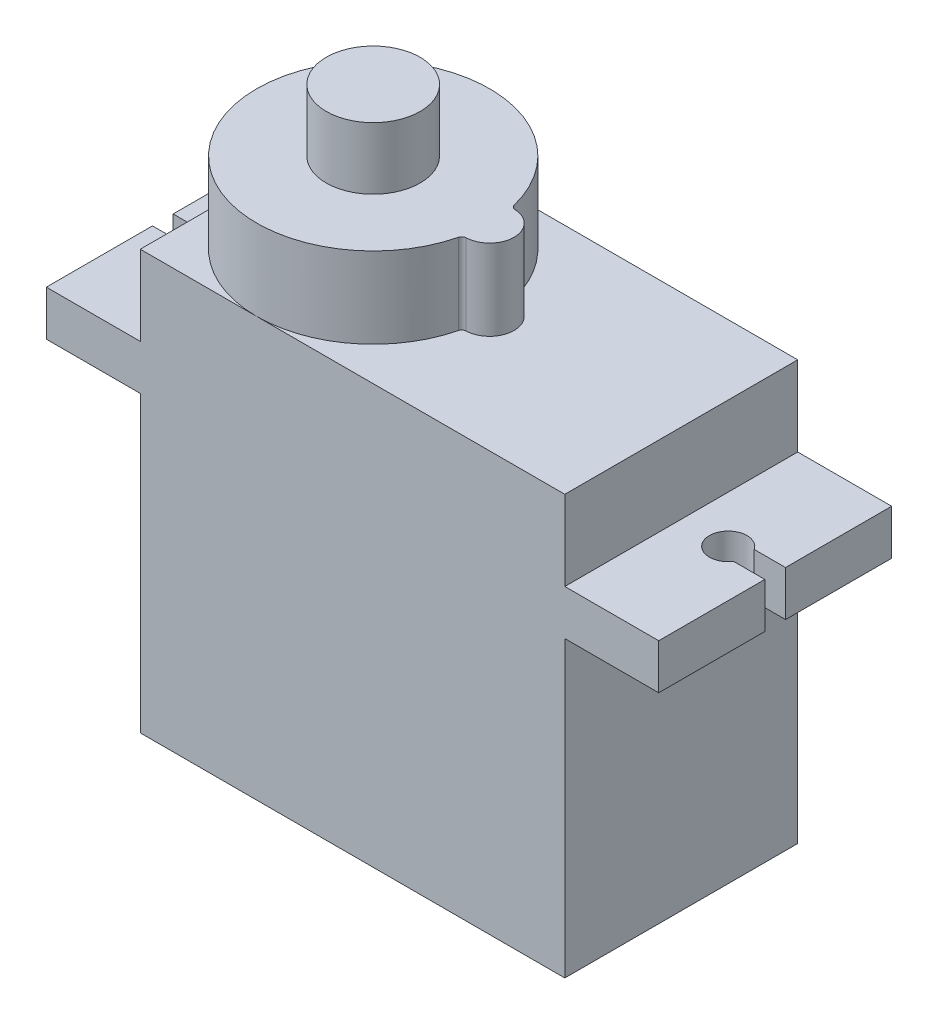
SolidWorks part; units mm, degrees
ref_plane "Front Plane" through (0, 0, 0) normal (0, 0, 1) x (1, 0, 0)
ref_plane "Top Plane" through (0, 0, 0) normal (0, 1, 0) x (1, 0, 0)
ref_plane "Right Plane" through (0, 0, 0) normal (1, 0, 0) x (0, 0, -1)
sketch "Sketch1" plane through (0, 0, 0) normal (0, 1, 0) x (1, 0, 0)
  line L1 (-11300, 6200) -> (11300, 6200)
  line L2 (-11300, 6200) -> (-11300, -6200)
  line L3 (-11300, -6200) -> (11300, -6200)
  line L4 (11300, 6200) -> (11300, -6200)
  line L5 (-11300, 6200) -> (11300, -6200) construction
  line L6 (-11300, -6200) -> (11300, 6200) construction
  point P0 (0, 0)
  dimension "D1" = 22600
  dimension "D2" = 12400
extrude "Boss-Extrude1" add sketch "Sketch1" along normal blind 22300
sketch "Sketch2" plane through (0, 0, 6200) normal (0, 0, 1) x (1, 0, 0)
  line L0 (-11300, 22300) -> (11300, 22300) construction
  line L1 (11300, 18050) -> (16300, 18050)
  line L2 (11300, 18050) -> (11300, 15650)
  line L3 (11300, 15650) -> (16300, 15650)
  line L4 (16300, 18050) -> (16300, 15650)
  line L5 (11300, 18050) -> (16300, 15650) construction
  line L6 (11300, 15650) -> (16300, 18050) construction
  line L7 (11300, 22300) -> (11300, 0) construction
  line L8 (0, 0) -> (0, 14577.6035) construction
  line L9 (-11300, 15650) -> (-16300, 18050) construction
  line L10 (-11300, 18050) -> (-16300, 15650) construction
  line L11 (-16300, 18050) -> (-16300, 15650)
  line L12 (-11300, 15650) -> (-16300, 15650)
  line L13 (-11300, 18050) -> (-11300, 15650)
  line L14 (-11300, 18050) -> (-16300, 18050)
  point P0 (13800, 16850)
  point P16 (-13800, 16850)
  dimension "D1" = 4250
  dimension "D2" = 2400
  dimension "D3" = 5000
extrude "Boss-Extrude2" add sketch "Sketch2" against normal up to vertex (12400 mm away)
sketch "Sketch3" plane through (0, 18050, 0) normal (0, 1, 0) x (1, 0, 0)
  line L0 (0, 8589.9803) -> (0, 0) construction
  line L1 (13800, 0) -> (0, 0) construction
  line L2 (14635.1647, 550) -> (16300, 550)
  line L3 (16300, 6200) -> (16300, -6200) construction
  line L4 (14635.1647, -550) -> (16300, -550)
  line L5 (16300, 550) -> (16300, -550)
  line L6 (-16300, 550) -> (-16300, -550)
  line L7 (-14635.1647, 550) -> (-16300, 550)
  line L8 (-14635.1647, -550) -> (-16300, -550)
  arc A0 (14635.1647, 550) -> (14635.1647, -550) centre (13800, 0) ccw
  arc A1 (-14635.1647, 550) -> (-14635.1647, -550) centre (-13800, 0) cw
  dimension "D1" = 2500
  dimension "D2" = 2000
  dimension "1.10" = 1100
extrude "Cut-Extrude1" cut sketch "Sketch3" against normal blind 22300
sketch "Sketch4" plane through (0, 22300, 0) normal (0, 1, 0) x (1, 0, 0)
  line L0 (-11300, 6200) -> (-11300, -6200) construction
  line L1 (11300, 6200) -> (-11300, 6200) construction
  arc A0 (918.6047, 1488.7572) -> (918.6047, -1488.7572) centre (-5100, 0) ccw
  arc A1 (1151.4048, -1298.9833) -> (1151.4048, 1298.9833) centre (1100, 0) ccw
  arc A2 (1151.4048, -1298.9833) -> (918.6047, -1488.7572) centre (1161.2903, -1548.7878) ccw
  arc A3 (1151.4048, 1298.9833) -> (918.6047, 1488.7572) centre (1161.2903, 1548.7878) cw
  dimension "D1" = 12400
  dimension "D2" = 2600
  dimension "D3" = 250
extrude "Boss-Extrude3" add sketch "Sketch4" along normal blind 4300
sketch "Sketch5" plane through (0, 26600, 0) normal (0, 1, 0) x (1, 0, 0)
  circle A0 centre (-5100, 0) radius 2500
  dimension "D1" = 5000
extrude "Boss-Extrude4" add sketch "Sketch5" along normal blind 3300
sketch "Sketch6" plane through (-11300, 0, 0) normal (-1, 0, 0) x (0, 0, 1)
  line L0 (0, 4500) -> (0, 0) construction
  line L1 (-6200, 0) -> (6200, 0) construction
  circle A0 centre (0, 4500) radius 600
  circle A3 centre (1199.9998, 4499.2396) radius 600
  circle A4 centre (-1199.9998, 4499.2332) radius 600
  point P10 (0, 0)
  dimension "D2" = 1200
  dimension "D1" = 4500
  dimension "D3" = 4499.2332
extrude "Boss-Extrude5" add sketch "Sketch6" along normal blind 2300 separate body
